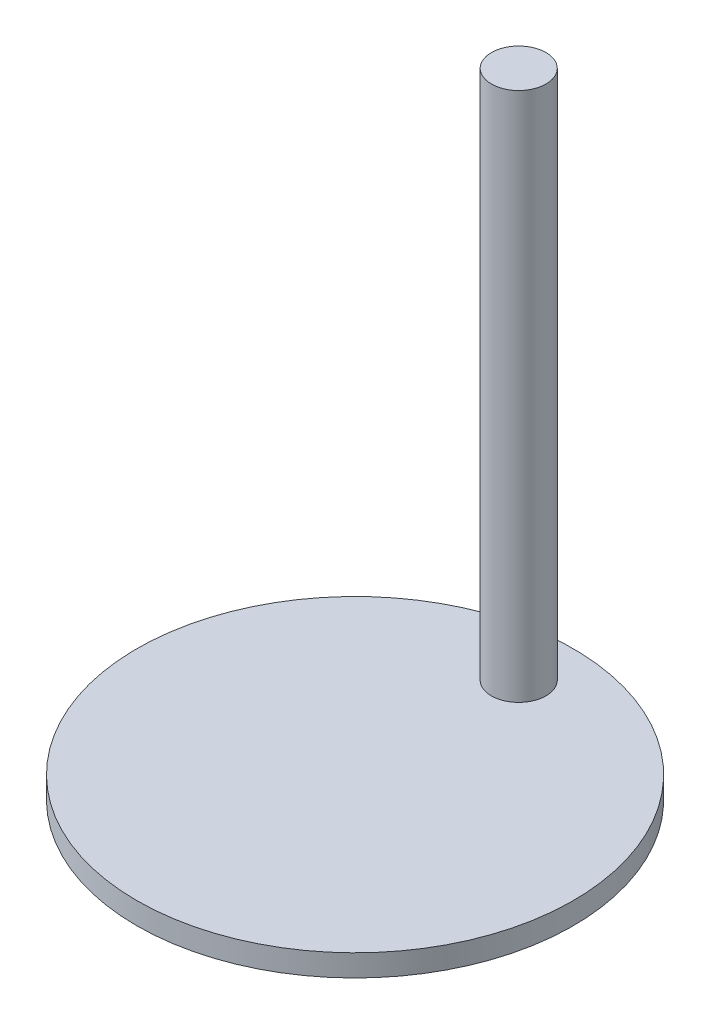
SolidWorks part; units mm, degrees
ref_plane "Front Plane" through (0, 0, 0) normal (0, 0, 1) x (1, 0, 0)
ref_plane "Top Plane" through (0, 0, 0) normal (0, 1, 0) x (1, 0, 0)
ref_plane "Right Plane" through (0, 0, 0) normal (1, 0, 0) x (0, 0, -1)
sketch "Sketch1" plane through (0, 0, 0) normal (0, 1, 0) x (1, 0, 0)
  line L0 (0, 5.08) -> (0, -5.08) construction
  circle A0 centre (0, 0) radius 5.08
  circle A1 centre (0, 3.81) radius 0.635
  dimension "D1" = 10.16
  dimension "D2" = 1.27
  dimension "D3" = 1.27
extrude "Boss-Extrude1" add sketch "Sketch1" along normal blind 0.508
sketch "Sketch2" plane through (0, 0, 0) normal (0, 1, 0) x (1, 0, 0)
  line L0 (0, 4.445) -> (0, 3.175) construction
  line L1 (-0.635, 3.81) -> (0.635, 3.81) construction
  circle A0 centre (0, 3.81) radius 0.635 construction
  circle A1 centre (0, 3.81) radius 0.635
extrude "Boss-Extrude2" add sketch "Sketch2" along normal blind 12.8445
